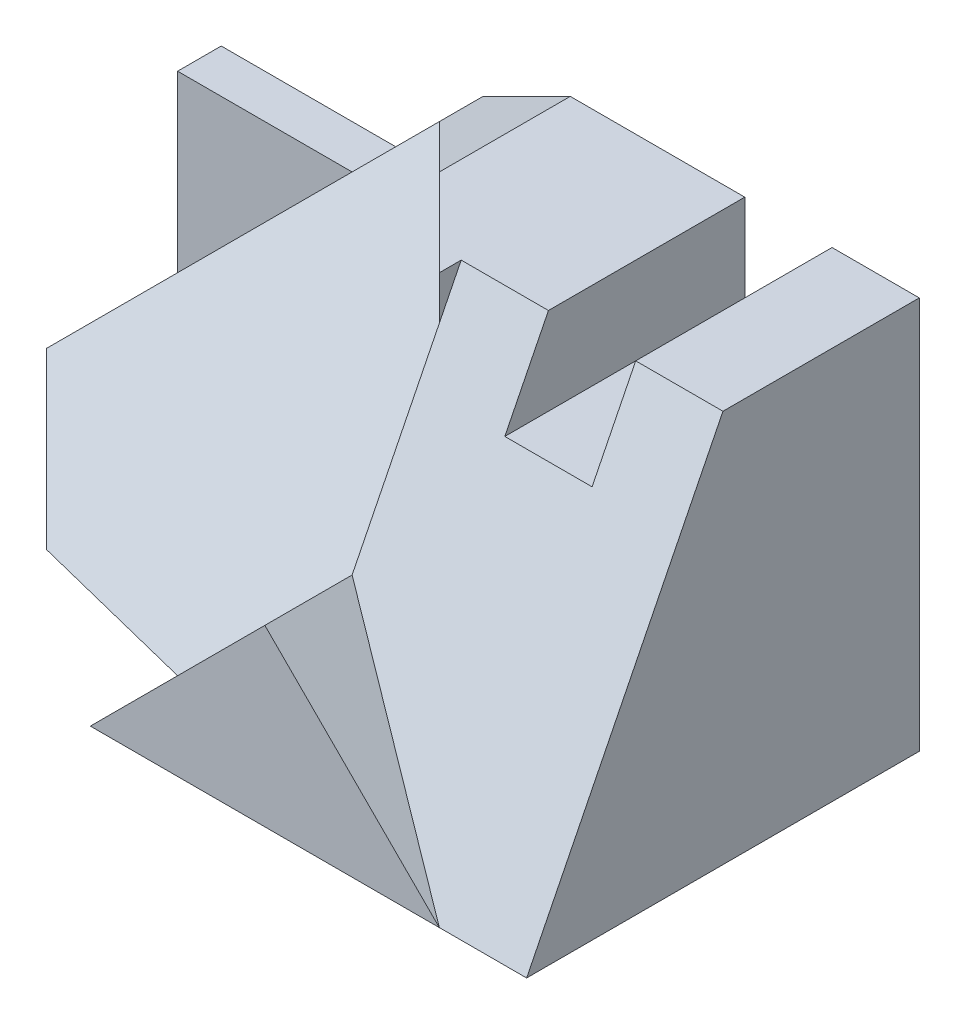
SolidWorks part; units mm, degrees
ref_plane "Front" through (0, 0, 0) normal (0, 0, 1) x (1, 0, 0)
ref_plane "Top" through (0, 0, 0) normal (0, 1, 0) x (1, 0, 0)
ref_plane "Right" through (0, 0, 0) normal (1, 0, 0) x (0, 0, -1)
sketch "Sketch1" plane through (0, 0, 0) normal (0, 1, 0) x (1, 0, 0)
  line L0 (-8, 0.5) -> (-6, -1.5)
  line L1 (-8, -4.5) -> (8, -4.5)
  line L2 (-8, -4.5) -> (-8, 4.5)
  line L3 (-8, 4.5) -> (8, 4.5)
  line L4 (8, -4.5) -> (8, 4.5)
  line L5 (-8, -4.5) -> (8, 4.5) construction
  line L6 (-8, 4.5) -> (8, -4.5) construction
  line L7 (-6, -1.5) -> (-2, -2.5)
  line L8 (-2, -2.5) -> (-2, -4.5)
  line L9 (-2, -4.5) -> (-8, -4.5)
  point P0 (0, 0)
  dimension "D1" = 9
  dimension "D2" = 16
  dimension "D3" = 2
  dimension "D4" = 1
  dimension "D5" = 4
  dimension "D6" = 2
  dimension "D7" = 2
extrude "Boss-Extrude1" add sketch "Sketch1" along normal blind 9 contours L7 L8 L1 L4 L3 L2 L0
sketch "Sketch2" plane through (0, 0, 4.5) normal (0, 0, 1) x (1, 0, 0)
  line L0 (-2, 9) -> (8, 9) construction
  line L1 (6, 9) -> (4, 9)
  line L2 (6, 9) -> (6, 7)
  line L3 (6, 7) -> (4, 7)
  line L4 (4, 9) -> (4, 7)
  line L5 (8, 9) -> (8, 0) construction
  line L6 (-8, 6) -> (-4, 6)
  line L7 (-8, 9) -> (-8, 0) construction
  line L8 (-4, 6) -> (-2, 8)
  line L9 (-2, 8) -> (0, 9)
  line L10 (0, 9) -> (-8, 9)
  line L11 (-8, 9) -> (-8, 6)
  line L12 (-8, 2) -> (-6, 0)
  line L13 (-6, 0) -> (-8, 0)
  line L14 (-8, 0) -> (-8, 2)
  dimension "D1" = 2
  dimension "D2" = 2
  dimension "D3" = 2
  dimension "D4" = 8
  dimension "D5" = 2
  dimension "D6" = 1
  dimension "D7" = 2
  dimension "D8" = 2
  dimension "D9" = 2
extrude "Cut-Extrude1" cut sketch "Sketch2" against normal blind 9
sketch "Sketch4" plane through (0, 0, 4.5) normal (0, 0, 1) x (1, 0, 0)
  line L0 (-4, 6) -> (-8, 2)
  line L1 (-8, 2) -> (-8, 6)
  line L2 (-8, 6) -> (-4, 6)
extrude "Cut-Extrude2" cut sketch "Sketch4" against normal blind 8
sketch3d "3DSketch1"
  line L0 (8, 0, 4.5) -> (6, 0, 4.5)
  line L1 (-2, 0, 4.5) -> (8, 0, 4.5) construction
  line L2 (6, 0, 4.5) -> (2, 4, 2.5)
  line L3 (8, 9, 4.5) -> (8, 9, -4.5) construction
  line L4 (0, 9, -4.5) -> (4, 9, -4.5) construction
  line L5 (2, 4, 2.5) -> (2, 9, 0)
  line L6 (2, 9, 0) -> (8, 9, 0)
  line L7 (8, 9, 0) -> (8, 0, 4.5)
  point P6 (8, 9, 0)
  point P7 (2, 9, 0)
  dimension "D1" = 2
  dimension "D2" = 6
  dimension "D3" = 7
  dimension "D4" = 4
  dimension "D5" = 4.5
  dimension "D6" = 4.5
  dimension "D7" = 6
extrude "Cut-Extrude3" cut sketch "3DSketch1" along direction (0, 0, -1) on the side against the normal blind 8
sketch3d "3DSketch2"
  line L0 (-2, 0, 4.5) -> (2, 4, 4.5)
  line L1 (2, 4, 4.5) -> (2, 4, 0.5)
  line L2 (2, 4, 0.5) -> (-2, 0, 2.5)
  line L3 (-2, 0, 2.5) -> (-2, 0, 4.5)
  dimension "D1" = 5
  dimension "D2" = 4
  dimension "D3" = 6
extrude "Cut-Extrude4" cut sketch "3DSketch2" along direction (0, 1, 0) on the side against the normal blind 8
sketch3d "3DSketch3"
  line L1 (-2, 8, -4.5) -> (-2, 8, 2.5) construction
  line L2 (-2, 8, -3.5) -> (-8, 2, -0.5)
  line L3 (-8, 2, -0.5) -> (-6, 0, 1.5)
  line L4 (-6, 0, 1.5) -> (-2, 0, 2.5)
  line L8 (-2, 0, 2.5) -> (2, 4, 0.5)
  line L9 (2, 4, 0.5) -> (-2, 8, -3.5)
  dimension "D1" = 1
extrude "Cut-Extrude5" cut sketch "3DSketch3" along direction (0, 1, 0) on the side of the normal blind 8 contours L2 L3 L4 L8 L9
